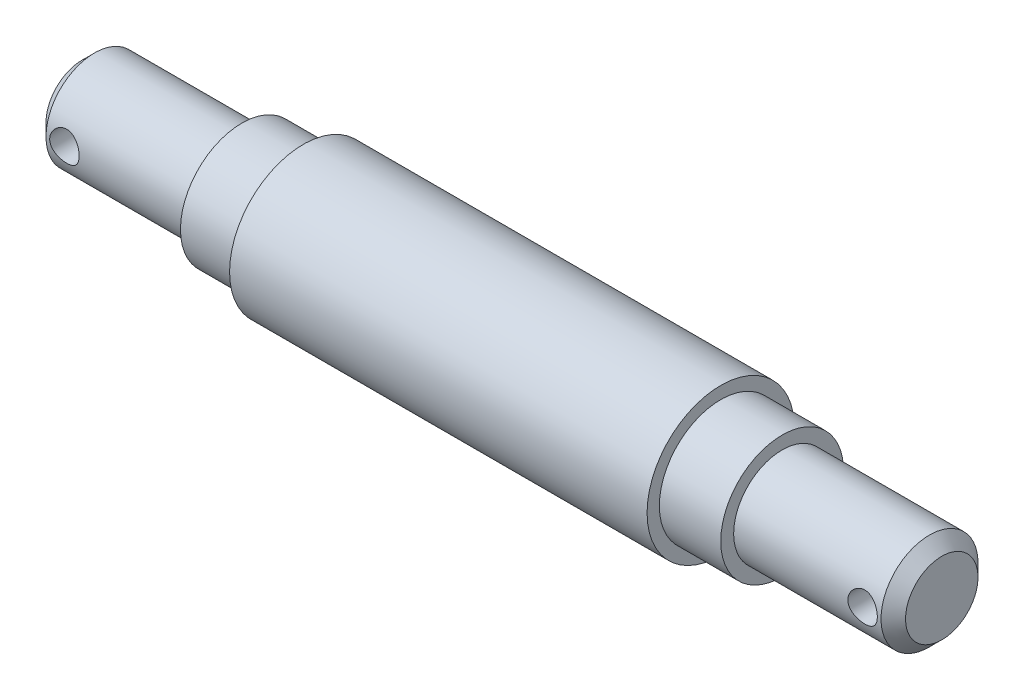
SolidWorks part; units mm, degrees
ref_plane "Płaszczyzna przednia" through (0, 0, 0) normal (0, 0, 1) x (1, 0, 0)
ref_plane "Płaszczyzna górna" through (0, 0, 0) normal (0, 1, 0) x (1, 0, 0)
ref_plane "Płaszczyzna prawa" through (0, 0, 0) normal (1, 0, 0) x (0, 0, -1)
sketch "Szkic1" plane through (0, 0, 0) normal (0, 0, 1) x (1, 0, 0)
  line L0 (0, 0) -> (70, 0)
  line L1 (70, 0) -> (70, 2.95)
  line L2 (69, 3.95) -> (57, 3.95)
  line L3 (57, 3.95) -> (57, 5)
  line L4 (57, 5) -> (52, 5)
  line L5 (52, 5) -> (52, 6)
  line L6 (52, 6) -> (18, 6)
  line L7 (18, 6) -> (18, 5)
  line L8 (18, 5) -> (13, 5)
  line L9 (13, 5) -> (13, 3.95)
  line L10 (13, 3.95) -> (1, 3.95)
  line L11 (0, 2.95) -> (0, 0)
  line L12 (1, 3.95) -> (0, 2.95)
  line L13 (70, 2.95) -> (69, 3.95)
  point P4 (70, 3.95)
  point P13 (0, 3.95)
  dimension "D1" = 70
  dimension "D2" = 13
  dimension "D3" = 5
  dimension "D4" = 3.95
  dimension "D5" = 5
  dimension "D6" = 6
revolve "Obrót1" add sketch "Szkic1" angle 360 about L0
sketch "Szkic2" plane through (0, 0, 0) normal (0, 0, 1) x (1, 0, 0)
  line L0 (70, -2.95) -> (70, 2.95) construction
  circle A0 centre (67.5, 0) radius 1.2
  circle A1 centre (2.5, 0) radius 1.2
  dimension "D2" = 2.4
  dimension "D3" = 2.4
  dimension "D1" = 2.5
  dimension "D4" = 2.5
extrude "Wytnij-wyciągnięcie1" cut sketch "Szkic2" against normal through all both and the other way through all contours A1 | A0
